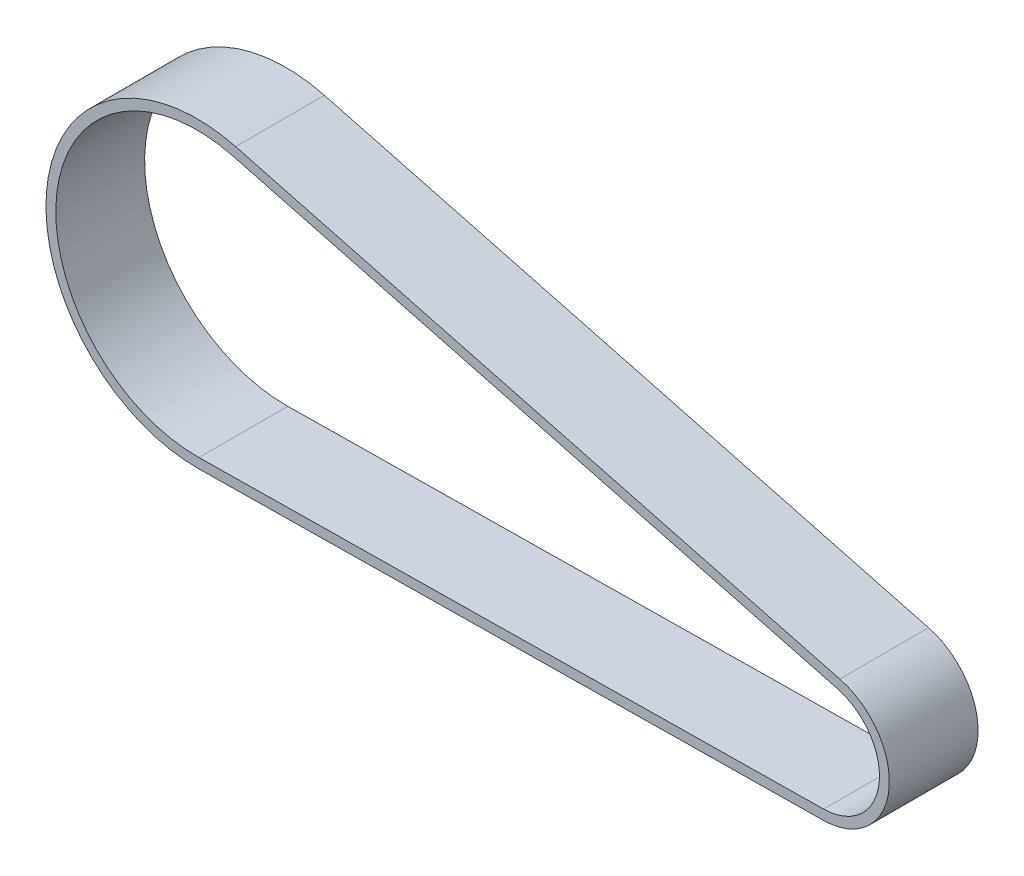
SolidWorks part; units mm, degrees
ref_plane "Ön Düzlem" through (0, 0, 0) normal (0, 0, 1) x (1, 0, 0)
ref_plane "Üst Düzlem" through (0, 0, 0) normal (0, 1, 0) x (1, 0, 0)
ref_plane "Sağ Düzlem" through (0, 0, 0) normal (1, 0, 0) x (0, 0, -1)
sketch "Sketch2" plane through (0, 0, 0) normal (0, 0, 1) x (1, 0, 0)
  line L0 (0, 0) -> (1, 0) construction
  line L1 (0, 0) -> (0, 1) construction
  line L2 (0.0723, -5.7295) -> (-63.2527, -6.5289)
  line L3 (-59.7868, 21.6582) -> (1.4582, 5.5413)
  arc A0 (1.4582, 5.5413) -> (0.0723, -5.7295) centre (0, 0) cw
  arc A1 (-63.2527, -6.5289) -> (-59.7868, 21.6582) centre (-63.4336, 7.8) cw
extrude "Extrude-Thin1" add sketch "Sketch2" along normal blind 4.5 and the other way blind 4.5 thin thin type one direction wall 1
